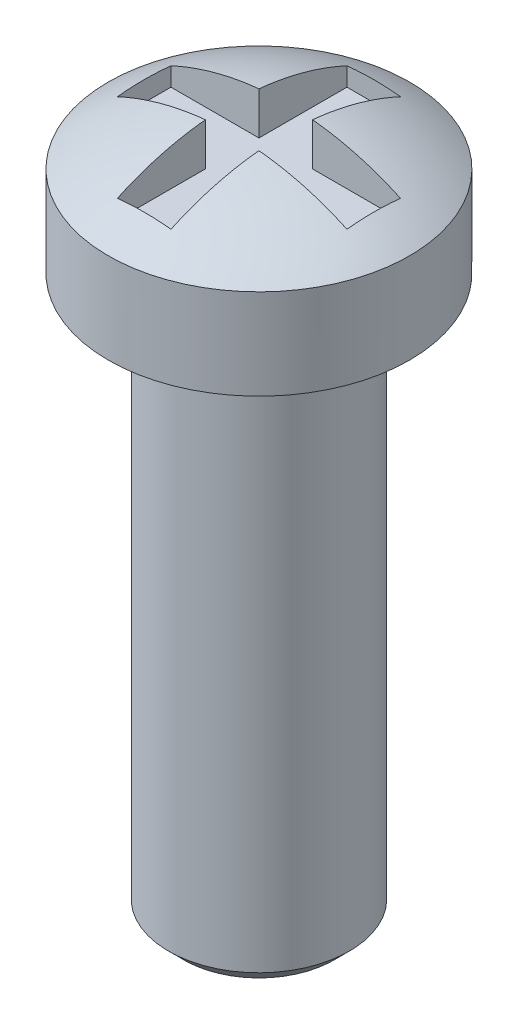
SolidWorks part; units mm, degrees
material "Chrome Stainless Steel"
ref_plane "Front Plane" through (0, 0, 0) normal (0, 0, 1) x (1, 0, 0)
ref_plane "Top Plane" through (0, 0, 0) normal (0, 1, 0) x (1, 0, 0)
ref_plane "Right Plane" through (0, 0, 0) normal (1, 0, 0) x (0, 0, -1)
sketch "Sketch1" plane through (0, 0, 0) normal (0, 0, 1) x (1, 0, 0)
  line L0 (0, 0) -> (0, -11.5)
  line L1 (0, -11.5) -> (1.5, -11.5)
  line L2 (1.5, -11.5) -> (1.5, -2.25)
  line L3 (1.5, -2.25) -> (2.5, -2.25)
  line L4 (2.5, -2.25) -> (2.5, -0.75)
  line L5 (0, 0) -> (-1.8819, 0) construction
  arc A0 (0, 0) -> (2.5, -0.75) centre (0, -4.5417) cw
  dimension "D1" = 11.5
  dimension "D2" = 2.5
  dimension "D3" = 1.5
  dimension "D4" = 1.5
  dimension "D5" = 9.25
revolve "Revolve1" add sketch "Sketch1" angle 360 about L0
sketch "Sketch2" plane through (0, 0, 0) normal (0, 0, 1) x (1, 0, 0)
  line L0 (0, -0.75) -> (0, -11.5) construction
  line L1 (-2.5, -0.75) -> (2.5, -0.75) construction
  line L2 (-1.5, -11.5) -> (1.5, -11.5) construction
  line L4 (-0.4445, -0.75) -> (0.4445, -0.75)
  line L5 (-0.4445, -0.75) -> (-0.4445, 0.8983)
  line L6 (-0.4445, 0.8983) -> (0.4445, 0.8983)
  line L7 (0.4445, -0.75) -> (0.4445, 0.8983)
  dimension "D1" = 0.889
extrude "Extrude1" cut sketch "Sketch2" against normal mid plane 3.81
sketch "Sketch3" plane through (0, 0, 0) normal (1, 0, 0) x (0, 0, -1)
  line L0 (0, -0.75) -> (0, -11.5) construction
  line L1 (-2.5, -0.75) -> (2.5, -0.75) construction
  line L2 (-1.5, -11.5) -> (1.5, -11.5) construction
  line L4 (-0.4445, -0.75) -> (0.4445, -0.75)
  line L5 (-0.4445, -0.75) -> (-0.4445, 1.6462)
  line L6 (-0.4445, 1.6462) -> (0.4445, 1.6462)
  line L7 (0.4445, -0.75) -> (0.4445, 1.6462)
  dimension "D1" = 0.889
extrude "Extrude2" cut sketch "Sketch3" against normal mid plane 3.81
chamfer "Chamfer1" distance 0.254 angle 45 1 edges at (-1.5, -11.5, 0)
